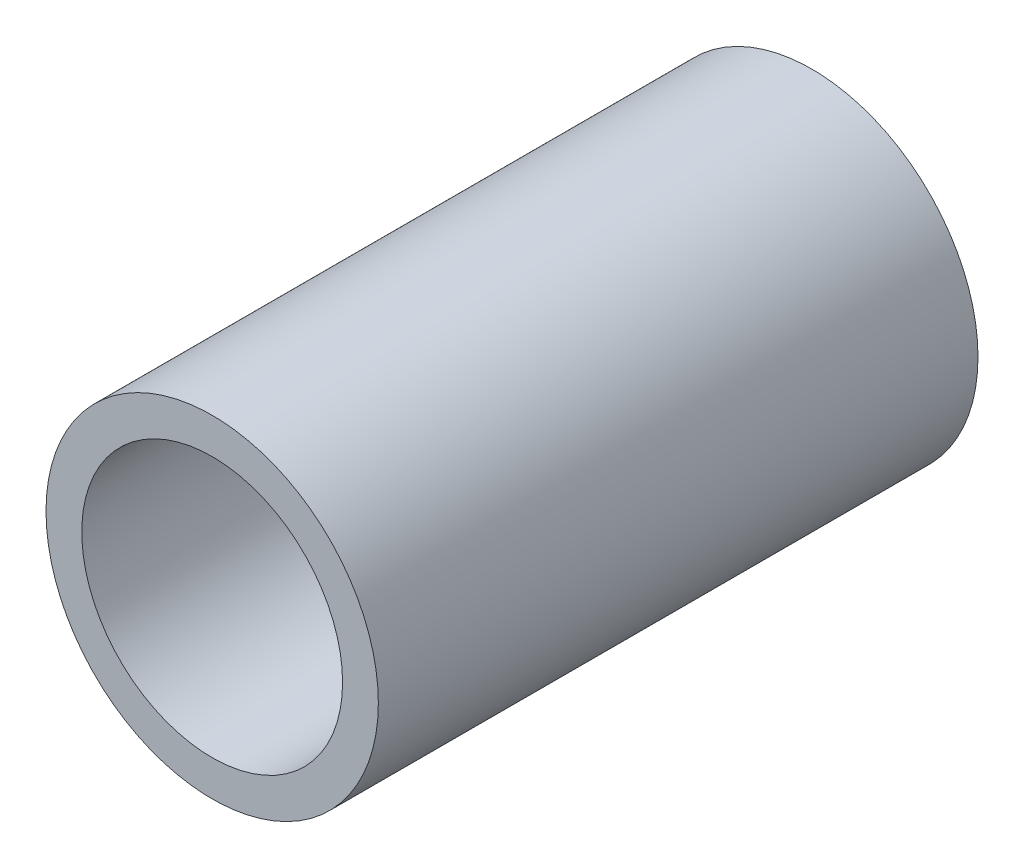
SolidWorks part; units mm, degrees
material "PVC 0.007 Plasticized"
ref_plane "Front Plane" through (0, 0, 0) normal (0, 0, 1) x (1, 0, 0)
ref_plane "Top Plane" through (0, 0, 0) normal (0, 1, 0) x (1, 0, 0)
ref_plane "Right Plane" through (0, 0, 0) normal (1, 0, 0) x (0, 0, -1)
sketch "Sketch1" plane through (0, 0, 0) normal (0, 0, 1) x (1, 0, 0)
  line L0 (10.4648, 0) -> (13.335, 0) construction
  circle A0 centre (0, 0) radius 13.335 construction
  circle A1 centre (0, 0) radius 10.4648 construction
  dimension "ID" = 20.9296
  dimension "OD" = 26.67
  dimension "Wall Thickness" = 2.8702
sketch "Sketch2" plane through (0, 0, 0) normal (1, 0, 0) x (0, 0, -1)
  line L0 (-762, 0) -> (762, 0) construction
  line L1 (-728.6625, 13.335) -> (-728.6625, -13.335) construction
  line L2 (728.6625, 13.335) -> (728.6625, -13.335) construction
  point P4 (0, 0)
  point P8 (-728.6625, 0)
  point P11 (728.6625, 0)
  dimension "Length" = 1524
  dimension "D1" = 33.3375
  dimension "D2" = 33.3375
  dimension "D3" = 26.67
sketch "Sketch3" plane through (0, 0, 0) normal (0, 0, 1) x (1, 0, 0)
  circle A0 centre (0, 0) radius 13.335
  circle A1 centre (0, 0) radius 13.335 construction
  circle A2 centre (0, 0) radius 10.4648 construction
  circle A3 centre (0, 0) radius 10.4648
extrude "Boss-Extrude1" add sketch "Sketch3" along normal up to vertex (762 mm away) and the other way up to vertex (762 mm away) up to point (0, 0, 762) other way up to point (0, 0, -762)
sketch "Sketch4" plane through (0, 0, 762) normal (0, 0, 1) x (1, 0, 0)
  circle A0 centre (0, 0) radius 10.4648 construction
  circle A1 centre (0, 0) radius 13.335 construction
  circle A2 centre (0, 0) radius 10.4648
  circle A3 centre (0, 0) radius 13.335
extrude "Cut-Extrude2" cut sketch "Sketch4" against normal offset from surface (1475.8779 mm away) 48.1221 contours A3 up to face at (10.4648, 0, -762)
equation "\"D1@Sketch2\"=\"OD@Sketch1\" * 1.25"
equation "\"D2@Sketch2\"=\"D1@Sketch2\""
equation "\"D3@Sketch2\"= \"OD@Sketch1\""
